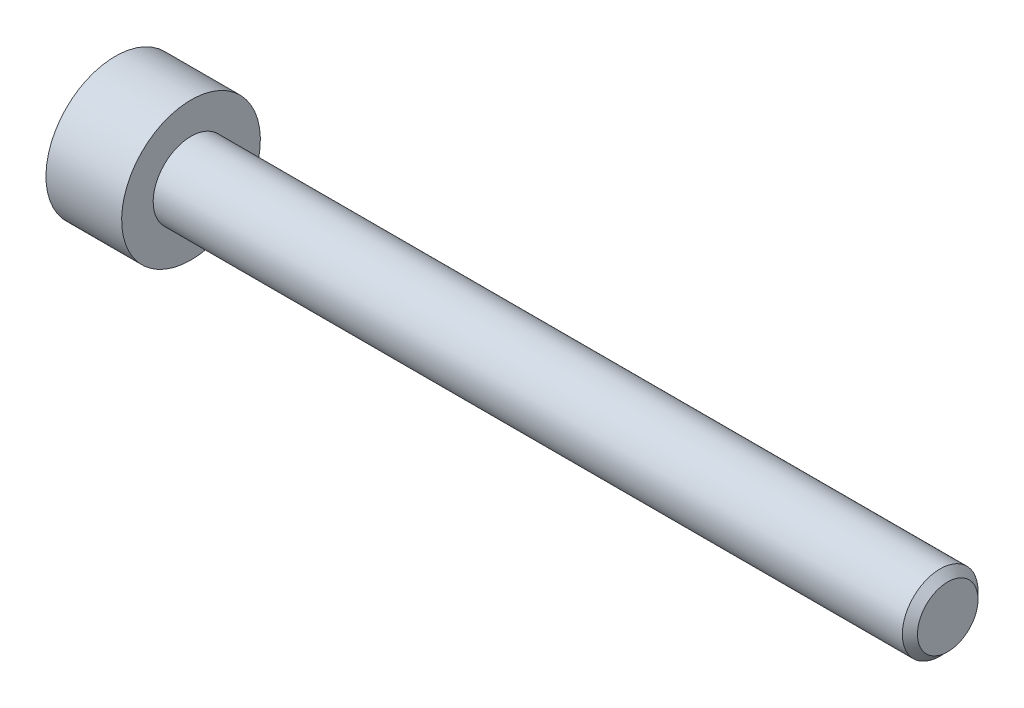
SolidWorks part; units mm, degrees
material "Plain Carbon Steel"
ref_plane "Front Plane" through (0, 0, 0) normal (0, 0, 1) x (1, 0, 0)
ref_plane "Top Plane" through (0, 0, 0) normal (0, 1, 0) x (1, 0, 0)
ref_plane "Right Plane" through (0, 0, 0) normal (1, 0, 0) x (0, 0, -1)
sketch "Sketch2" plane through (0, 0, 0) normal (1, 0, 0) x (0, 0, -1)
  circle A0 centre (0, 0) radius 1.5
  dimension "D1" = 3
extrude "Boss-Extrude1" add sketch "Sketch2" against normal blind 30
chamfer "Chamfer1" distance 0.3 angle 45 1 edges at (0, 0, -1.5)
sketch "Sketch6" plane through (0, 0, 0) normal (0, 0, 1) x (1, 0, 0)
  line L0 (-33, 0) -> (-33, 2.75)
  line L1 (-33, 0) -> (-30, 0)
  line L2 (-33, 2.75) -> (-30, 2.75)
  line L6 (-30, 2.75) -> (-30, 0)
  line L8 (-30, 0) -> (-14.6471, 0) construction
  line L10 (-30, 1.5) -> (-30, -1.5) construction
  dimension "D1" = 3
  dimension "D2" = 5.5
revolve "Revolve1" add sketch "Sketch6" angle 360 about L8
sketch "Sketch7" plane through (-33, 0, 0) normal (-1, 0, 0) x (0, 0, 1)
  line L1 (0, 1.4434) -> (-1.25, 0.7217)
  line L2 (-1.25, 0.7217) -> (-1.25, -0.7217)
  line L3 (-1.25, -0.7217) -> (0, -1.4434)
  line L4 (0, -1.4434) -> (1.25, -0.7217)
  line L5 (1.25, -0.7217) -> (1.25, 0.7217)
  line L6 (1.25, 0.7217) -> (0, 1.4434)
  circle A0 centre (0, 0) radius 1.25 construction
  dimension "D1" = 2.5
extrude "Cut-Extrude1" cut sketch "Sketch7" against normal blind 1.6
sketch "Sketch8" plane through (-33, 0, 0) normal (-1, 0, 0) x (0, 0, 1)
  circle A0 centre (0, 0) radius 1.4934
  dimension "D1" = 0.05
extrude "Cut-Extrude2" cut sketch "Sketch8" against normal blind 1 draft 45
